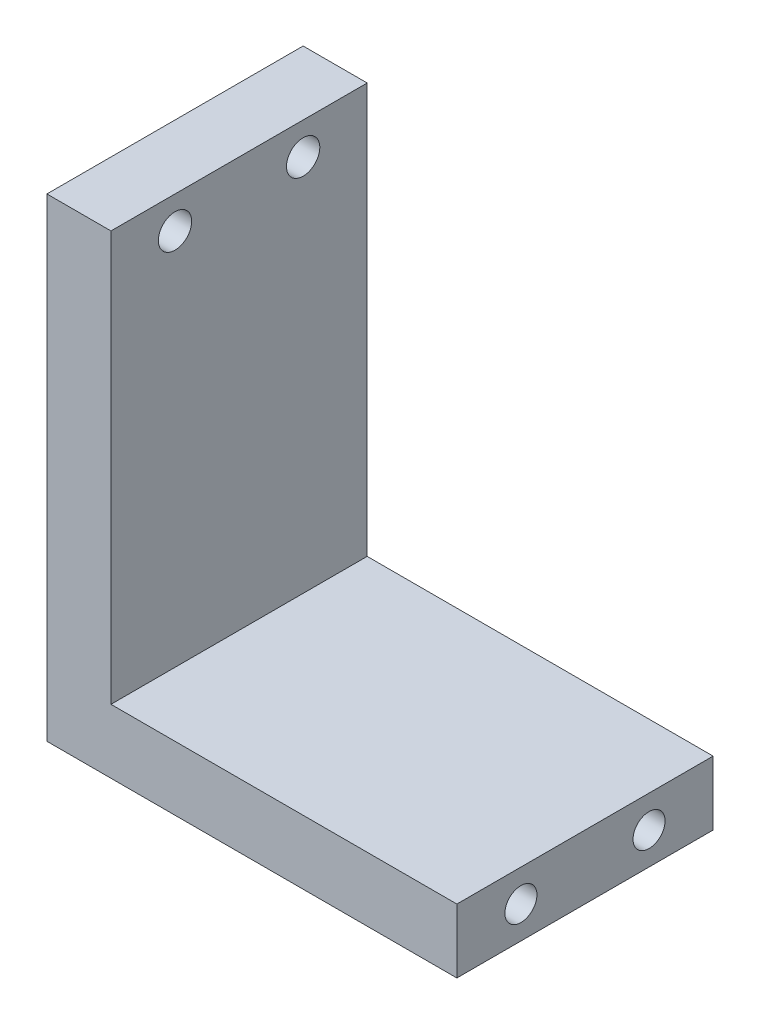
SolidWorks part; units mm, degrees
ref_plane "Plan de face" through (0, 0, 0) normal (1, 0, 0) x (0, 1, 0)
ref_plane "Plan de dessus" through (0, 0, 0) normal (0, 0, 1) x (0, 1, 0)
ref_plane "Plan de droite" through (0, 0, 0) normal (0, 1, 0) x (-1, 0, 0)
sketch "Esquisse1" plane through (0, 0, 0) normal (0, 0, 1) x (0, 1, 0)
  line L0 (0, 0) -> (32, 0)
  line L2 (0, 0) -> (0, -27)
  line L3 (0, -27) -> (-5, -27)
  line L4 (-5, 0) -> (-5, -27)
  line L6 (-5, 0) -> (-5, 5)
  line L7 (-5, 5) -> (32, 5)
  line L8 (32, 0) -> (32, 5)
  dimension "D3" = 32
extrude "Boss_Extrude_Equerre" add sketch "Esquisse1" along normal blind 20
hole_wizard "Fraisage pour vis à tête fraisée M21" positions "Esquisse6" profile "Esquisse3" countersink size "M2" standard "Ansi Metric" end condition through all
sketch "Esquisse6" plane through (-5, 0, 0) normal (-1, 0, 0) x (0, 0, 1)
  line L0 (20, 32) -> (0, 32) construction
  line L1 (0, 32) -> (0, -5) construction
  point P0 (15, 29.5)
  point P2 (5, 29.5)
  dimension "D1" = 2.5
  dimension "D3" = 15
sketch "Esquisse3" plane through (-5, 29.5, 15) normal (0, 1, 0) x (0, 0, 1)
  line L0 (0, 0) -> (0, 32)
  line L1 (0, 32) -> (1.3, 32)
  line L2 (1.3, 32) -> (1.3, 0.9)
  line L3 (1.3, 0.9) -> (2.2, 0)
  line L5 (2.2, 0) -> (0, 0)
  line L6 (-1.3, 0.9) -> (-2.2, 0) construction
  line L11 (0, -6.35) -> (0, 107.95) construction
  dimension "Diamètre du perçage jusqu'au prochain" = 2.6
  dimension "Profondeur du perçage jusqu'au prochain" = 32
  dimension "Diamètre du fraisage entrant" = 4.4
  dimension "Angle du fraisage entrant" = 90
hole_wizard "Trou taraudé M3x0.51" positions "Esquisse7" profile "Esquisse8" tap size "M3x0.5" standard "Ansi Metric"
sketch "Esquisse7" plane through (27, 0, 0) normal (1, 0, 0) x (0, 1, 0)
  line L0 (-5, 20) -> (-5, 0) construction
  line L1 (-5, 0) -> (0, 0) construction
  point P0 (-2.5, 15)
  point P2 (-2.5, 5)
  point P7 (0, 0)
  point P12 (0, 0)
  point P15 (0, 0)
  dimension "D1" = 2.5
  dimension "D3" = 15
sketch "Esquisse8" plane through (27, -2.5, 15) normal (0, 1, 0) x (0, 0, -1)
  line L0 (0, 0) -> (0, 10.7511)
  line L1 (0, 10.7511) -> (1.25, 10)
  line L2 (1.25, 10) -> (1.25, 0)
  line L5 (1.25, 0) -> (0, 0)
  line L10 (0, 10.7511) -> (-1.25, 10) construction
  line L11 (0, -6.35) -> (0, 107.95) construction
  dimension "Diamètre du trou pour taraudage" = 2.5
  dimension "Profondeur du trou pour taraudage" = 10
  dimension "Angle de pointe" = 118
cosmetic thread "Filetage de perçage1"
cosmetic thread "Filetage de perçage2"
equation "\"Plaque_L\" = 37mm'longueur plaque"
equation "\"Plaque_H\" = 37mm'largeur plaque"
equation "\"Plaque_E\"= 2mm'épaisseur plaque"
equation "\"Trou_R\"= 1.2mm'rayon perforation base"
equation "\"Trou_dx\"= 4mm'distance entre trou sur x"
equation "\"Trou-dy\"= 4mm'distance entre trou sur y"
equation "\"Cavite_H\" = 20mm'hauteur cavité"
equation "\"Cavite_L\" = 32mm'largeur cavité"
equation "\"Cavite_E\"= 5mm'épaisseur cavité"
equation "\"Offset_Z\"= 0mm"
equation "\"D2@Esquisse1\"=\"Cavite_E\""
equation "\"D3@Esquisse1\"=\"Cavite_L\""
equation "\"D1@Esquisse1\"=\"Cavite_largeur\""
equation "\"Vis_Diam\" = 1.6mm"
equation "\"Offset_Bord\" = \"Cavite_E\" / 2"
equation "\"Vis_Long\"= 5mm"
equation "\"Perc_Passage\"= 1.8mm"
equation "\"Perc_Taraud\" = 1.3mm"
equation "\"Fraisure_Diam\"= 3mm"
equation "\"Fraisure_Prof\" = 1mm"
equation "\"Offset_hauteur_vis1\"= \"Cavite_E\""
equation "\"Offset_hauteur_vis2\"= \"Cavite_H\" - \"Cavite_E\""
equation "\"Perc_Profondeur\" = \"Cavite_E\""
equation "\"Taraud_Profondeur\" = \"Cavite_E\""
equation "\"D1@Esquisse6\"=\"Offset_Bord\""
equation "\"D2@Esquisse6\"=\"Offset_hauteur_vis1\""
equation "\"D3@Esquisse6\"=\"Offset_hauteur_vis2\""
equation "\"Cavite_largeur\"= 27mm'hauteur cavité"
equation "\"D1@Boss_Extrude_Equerre\"=\"Cavite_H\""
equation "\"D1@Esquisse7\"=-\"Offset_Bord\""
equation "\"D2@Esquisse7\"=\"Offset_hauteur_vis1\""
equation "\"D3@Esquisse7\"=\"Offset_hauteur_vis2\""
